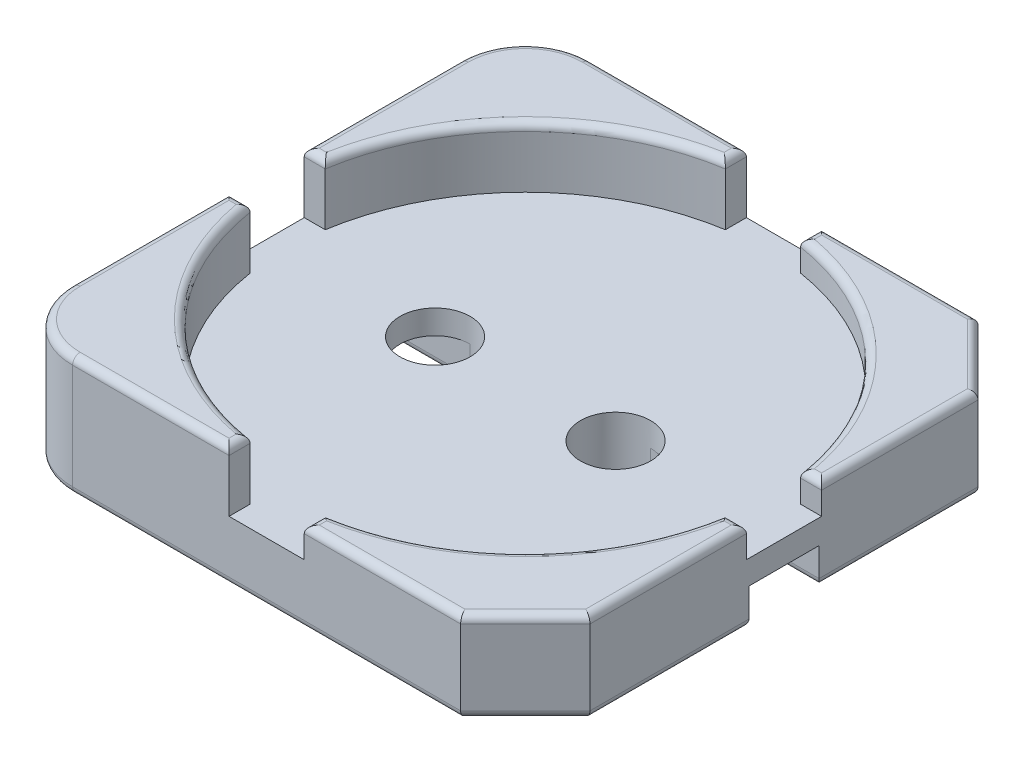
SolidWorks part; units mm, degrees
ref_plane "Alzado" through (0, 0, 0) normal (0, 0, 1) x (1, 0, 0)
ref_plane "Planta" through (0, 0, 0) normal (0, 1, 0) x (1, 0, 0)
ref_plane "Vista lateral" through (0, 0, 0) normal (1, 0, 0) x (0, 0, -1)
sketch "Croquis2" plane through (0, 0, 0) normal (0, 1, 0) x (1, 0, 0)
  line L0 (1.6125, 2.15) -> (2.15, 1.6125)
  line L1 (-1.6125, -2.15) -> (1.6125, -2.15)
  line L2 (-2.15, -1.6125) -> (-2.15, 1.6125)
  line L3 (-1.6125, 2.15) -> (1.6125, 2.15)
  line L4 (2.15, -1.6125) -> (2.15, 1.6125)
  line L5 (-2.15, -2.15) -> (2.15, 2.15) construction
  line L6 (-2.15, 2.15) -> (2.15, -2.15) construction
  line L7 (1.6125, -2.15) -> (2.15, -1.6125)
  line L9 (1.6125, -2.15) -> (2.15, -1.6125) construction
  arc A0 (-2.15, 1.6125) -> (-1.6125, 2.15) centre (-1.6125, 1.6125) cw
  arc A1 (-1.6125, -2.15) -> (-2.15, -1.6125) centre (-1.6125, -1.6125) cw
  arc A3 (-2.15, -1.6125) -> (-1.6125, -2.15) centre (-1.6125, -1.6125) ccw construction
  point P0 (0, 0)
extrude "Saliente-Extruir1" add sketch "Croquis2" along normal up to vertex (1 mm away)
sketch "Croquis3" plane through (0, 1, 0) normal (0, 1, 0) x (1, 0, 0)
  line L0 (2.3289, 0) -> (-2.2631, 0) construction
  line L1 (-1.9754, 0.3125) -> (-2.15, 0.3125)
  line L2 (0, 1.7302) -> (0, -2.0879) construction
  line L3 (-2.15, -1.6125) -> (-2.15, 1.6125) construction
  line L4 (-1.9754, -0.3125) -> (-2.15, -0.3125)
  line L5 (0.3125, 1.9754) -> (0.3125, 2.15)
  line L6 (-0.3125, 1.9754) -> (-0.3125, 2.15)
  line L7 (1.9754, -0.3125) -> (2.15, -0.3125)
  line L8 (1.9754, 0.3125) -> (2.15, 0.3125)
  line L9 (-0.3125, -1.9754) -> (-0.3125, -2.15)
  line L10 (0.3125, -1.9754) -> (0.3125, -2.15)
  line L11 (1.6125, 2.15) -> (-1.6125, 2.15) construction
  line L13 (-2.65, 0.25) -> (-0.75, 0.25) construction
  line L16 (2.15, -1.6125) -> (2.15, 1.6125)
  line L17 (1.6125, 2.15) -> (-1.6125, 2.15)
  line L18 (-2.15, 1.6125) -> (-2.15, -1.6125)
  line L19 (-1.6125, -2.15) -> (1.6125, -2.15)
  line L20 (2.15, -1.6125) -> (2.15, 1.6125)
  line L21 (1.6125, 2.15) -> (-1.6125, 2.15)
  line L22 (-2.15, 1.6125) -> (-2.15, -1.6125)
  line L23 (-1.6125, -2.15) -> (1.6125, -2.15)
  line L26 (1.6125, -2.15) -> (2.15, -1.6125)
  line L27 (1.6125, -2.15) -> (2.15, -1.6125)
  line L28 (2.15, 1.6125) -> (1.6125, 2.15)
  line L29 (2.15, 1.6125) -> (1.6125, 2.15)
  arc A0 (-1.9754, -0.3125) -> (-0.3125, -1.9754) centre (0, 0) ccw
  arc A1 (0.3125, -1.9754) -> (1.9754, -0.3125) centre (0, 0) ccw
  arc A2 (1.9754, 0.3125) -> (0.3125, 1.9754) centre (0, 0) ccw
  arc A3 (-0.3125, 1.9754) -> (-1.9754, 0.3125) centre (0, 0) ccw
  circle A4 centre (0, 0) radius 2 construction
  arc A6 (-1.6125, 2.15) -> (-2.15, 1.6125) centre (-1.6125, 1.6125) ccw
  arc A7 (-1.6125, 2.15) -> (-2.15, 1.6125) centre (-1.6125, 1.6125) ccw
  arc A8 (-2.15, -1.6125) -> (-1.6125, -2.15) centre (-1.6125, -1.6125) ccw
  arc A9 (-2.15, -1.6125) -> (-1.6125, -2.15) centre (-1.6125, -1.6125) ccw
  point P14 (-5.15, 0.793)
  point P28 (0, 0)
  line M16 (2.15, -1.6125) -> (2.15, 1.6125)
  line M17 (1.6125, 2.15) -> (-1.6125, 2.15)
  line M18 (-2.15, 1.6125) -> (-2.15, -1.6125)
  line M19 (-1.6125, -2.15) -> (1.6125, -2.15)
  dimension "D1" = 0.0625
  dimension "D2" = 4
  dimension "D3" = 0
extrude "Cortar-Extruir1" cut sketch "Croquis3" against normal blind 0.5 contours L6 A3 L1 L4 A0 L9 L10 A1 L7 L8 A2 L5 M18 M19 M16 M17
sketch "Croquis4" plane through (0, 1, 0) normal (0, 1, 0) x (1, 0, 0)
  line L0 (2.15, -1.6125) -> (2.15, 1.6125) construction
  line L6 (2.15, 2.15) -> (0, 2.15)
  line L7 (2.15, 2.15) -> (2.15, -2.15)
  line L8 (2.15, -2.15) -> (0, -2.15)
  line L9 (0, 2.15) -> (0, -2.15)
  line L11 (-0.3125, -2.15) -> (0.3125, -2.15) construction
extrude "Cortar-Extruir2" cut sketch "Croquis4" against normal up to vertex (0.25 mm away)
sketch "Croquis5" plane through (0, 0, 0) normal (0, -1, 0) x (-1, 0, 0)
  line L0 (2.15, -0.2915) -> (0.75, -0.2915)
  line L1 (2.15, 0.2915) -> (0.75, 0.2915)
  line L2 (-6.4447, 0) -> (5.8226, 0) construction
  line L3 (0, -3.7688) -> (0, 4.0466) construction
  line L4 (2.15, 1.6125) -> (2.15, -1.6125) construction
  line L5 (-2.15, -1.6125) -> (-2.15, 1.6125) construction
  line L6 (-2.15, -0.2915) -> (-2.15, 0.2915)
  line L7 (2.15, -0.2915) -> (2.15, 0.2915)
  line L8 (-0.75, -0.2915) -> (-2.15, -0.2915)
  line L9 (-0.75, 0.2915) -> (-2.15, 0.2915)
  arc A0 (-0.75, -0.2915) -> (-0.75, 0.2915) centre (-0.75, 0) ccw
  arc A1 (0.75, -0.2915) -> (0.75, 0.2915) centre (0.75, 0) cw
  arc A2 (-0.75, -0.25) -> (-0.75, 0.25) centre (-0.75, 0) ccw construction
  point P13 (-0.6, 0.325)
  point P18 (-0.6, 0.25)
  point P28 (-1.0116, 0.1287)
extrude "Cortar-Extruir3" cut sketch "Croquis5" against normal blind 0.3
sketch "Croquis6" plane through (0, 0.5, 0) normal (0, 1, 0) x (1, 0, 0)
  line L0 (0, 1.7396) -> (0, -1.4977) construction
  circle A0 centre (0.75, 0) radius 0.2915
  circle A1 centre (-0.75, 0) radius 0.2915
  arc A2 (0.75, 0.2915) -> (0.75, -0.2915) centre (0.75, 0) ccw construction
  point P7 (0.75, 0.2915)
  point P11 (0, 0)
extrude "Cortar-Extruir4" cut sketch "Croquis6" against normal through all
fillet "Redondeo1" radius 0.0625 40 edges at (1.8812, 0.75, 1.8812) (0.9625, 0.75, 2.15) (1.4142, 0.75, 1.4142) (2.15, 0.75, 0.9625) (1.8812, 0.75, -1.8812) (2.15, 0.75, -0.9625) (1.4142, 0.75, -1.4142) (0.9625, 0.75, -2.15) (-1.4142, 1, -1.4142) (-2.15, 1, -0.9625) (-1.9926, 1, -1.9926) (-0.9625, 1, -2.15) (-1.9926, 1, 1.9926) (-2.15, 1, 0.9625) (-1.4142, 1, 1.4142) (-0.9625, 1, 2.15) (1.45, 0, -0.2915) (2.15, 0, -0.952) (1.8812, 0, -1.8812) (0, 0, -2.15) (-1.9926, 0, -1.9926) (-2.15, 0, -0.952) (-1.45, 0, -0.2915) (-0.4585, 0, 0) (-1.45, 0, 0.2915) (-2.15, 0, 0.952) (-1.9926, 0, 1.9926) (0, 0, 2.15) (1.8812, 0, 1.8813) (2.15, 0, 0.952) (1.45, 0, 0.2915) (0.4585, 0, 0) (0.3125, 0.75, 2.0627) (2.0627, 0.75, 0.3125) (2.0627, 0.75, -0.3125) (0.3125, 0.75, -2.0627) (-2.0627, 1, -0.3125) (-0.3125, 1, -2.0627) (-2.0627, 1, 0.3125) (-0.3125, 1, 2.0627)
